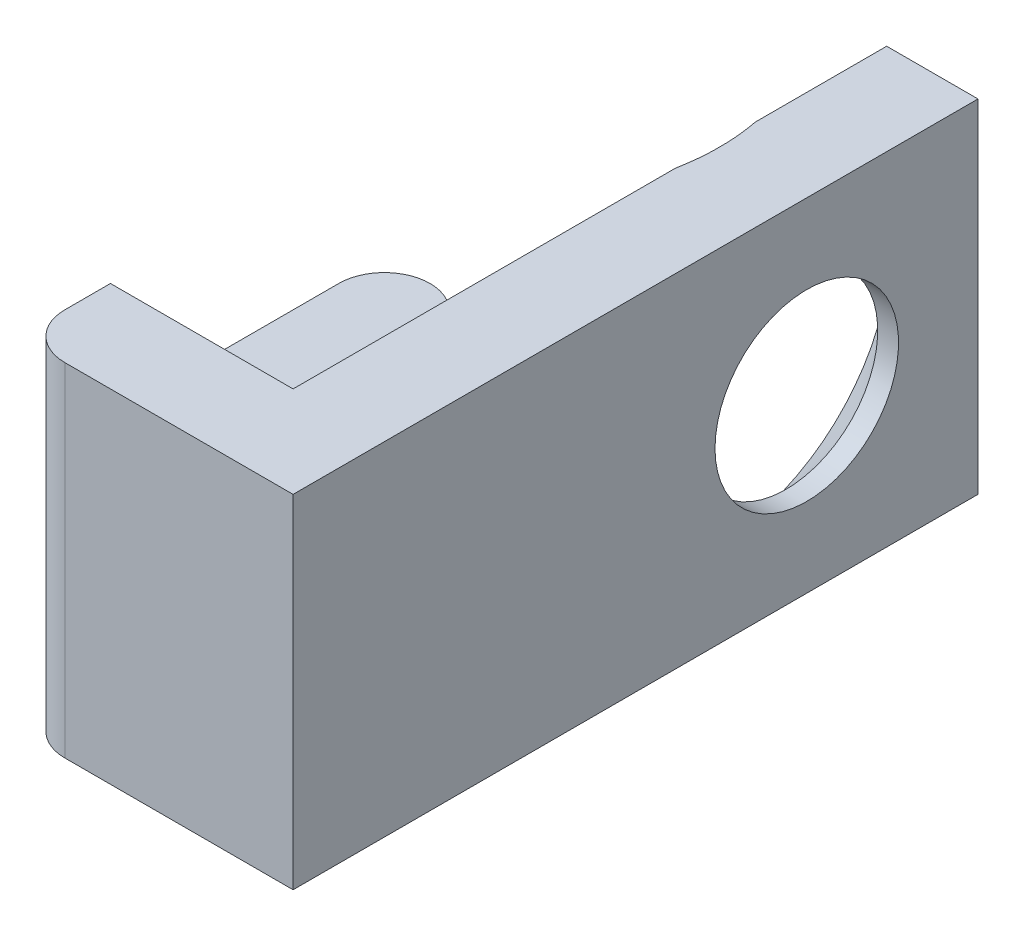
SolidWorks part; units mm, degrees
ref_plane "Front Plane" through (0, 0, 0) normal (0, 0, 1) x (1, 0, 0)
ref_plane "Top Plane" through (0, 0, 0) normal (0, 1, 0) x (1, 0, 0)
ref_plane "Right Plane" through (0, 0, 0) normal (1, 0, 0) x (0, 0, -1)
sketch "Sketch1" plane through (0, 0, 0) normal (0, 1, 0) x (1, 0, 0)
  line L0 (-1.27, -8.255) -> (-5.08, -8.255) construction
  line L1 (-1.27, -9.525) -> (1.27, -9.525)
  line L2 (-1.27, -9.525) -> (-1.27, 9.525)
  line L3 (-1.27, 9.525) -> (1.27, 9.525)
  line L4 (1.27, -9.525) -> (1.27, 9.525)
  line L5 (-1.27, -9.525) -> (1.27, 9.525) construction
  line L6 (-1.27, 9.525) -> (1.27, -9.525) construction
  line L7 (-1.27, -9.525) -> (-5.08, -9.525)
  line L8 (-1.27, -6.985) -> (-5.08, -6.985)
  line L9 (-5.08, -8.255) -> (-5.08, -0.635) construction
  line L10 (-6.35, -8.255) -> (-6.35, -0.635)
  line L11 (-3.81, -8.255) -> (-3.81, -0.635)
  arc A0 (-1.27, -9.525) -> (-1.27, -6.985) centre (-1.27, -8.255) ccw
  arc A1 (-5.08, -6.985) -> (-5.08, -9.525) centre (-5.08, -8.255) ccw
  arc A2 (-6.35, -8.255) -> (-3.81, -8.255) centre (-5.08, -8.255) ccw
  arc A3 (-3.81, -0.635) -> (-6.35, -0.635) centre (-5.08, -0.635) ccw
  point P0 (0, 0)
  point P8 (-3.175, -8.255)
  point P13 (-5.08, -4.445)
  point P20 (-3.9688, -2.2199)
  dimension "D1" = 2.54
  dimension "D2" = 19.05
  dimension "D3" = 2.54
  dimension "D4" = 2.54
  dimension "D5" = 6.35
extrude "Boss-Extrude1" add sketch "Sketch1" along normal mid plane 9.525 contours L11 A3 L10 A1 L8 | A1 A2 L11 L8 | A2 L7 L2 L8 L11 | L2 A0 | A0 L1 L4 L3 L2
sketch "Sketch2" plane through (-1.27, 0, 0) normal (-1, 0, 0) x (0, 0, 1)
  line L0 (-9.525, 0) -> (-4.7625, 0) construction
  line L1 (-9.525, 4.7625) -> (-9.525, -4.7625) construction
  line L2 (-9.525, -4.7625) -> (-4.7625, 0) construction
  line L3 (-4.7625, 0) -> (-9.525, 4.7625) construction
  point P10 (-4.7625, 0)
hole_wizard "CSK for #10 Flat Head Machine Screw (100)1" positions "3DSketch1" profile "Sketch3" countersink size "#10" standard "ANSI Inch" end condition through all
sketch3d "3DSketch1"
  point P0 (-1.27, 0, -4.7625)
sketch "Sketch3" plane through (-1.27, 0, -4.7625) normal (0, 1, 0) x (0, 0, 1)
  line L0 (0, 0) -> (0, 2.54)
  line L1 (0, 2.54) -> (2.5527, 2.54)
  line L2 (2.5527, 2.54) -> (2.5527, 1.9608)
  line L3 (2.5527, 1.9608) -> (4.8895, 0)
  line L5 (4.8895, 0) -> (0, 0)
  line L6 (-2.5527, 1.9608) -> (-4.8895, 0) construction
  line L11 (0, -6.35) -> (0, 107.95) construction
  dimension "Thru Hole Dia." = 5.1054
  dimension "Thru Hole Depth" = 2.54
  dimension "Near C'Sink Dia." = 9.779
  dimension "Near C'Sink Angle" = 100
sketch "Sketch4" plane through (0, 0, 0) normal (1, 0, 0) x (0, 0, -1)
  line L0 (0.635, -4.7625) -> (-3.81, -4.7625) construction
  line L1 (-8.255, -4.7625) -> (-0.635, -4.7625) construction
  line L2 (0.635, -7.9375) -> (-3.81, -7.9375)
  line L3 (0.635, -1.5875) -> (-3.81, -1.5875)
  line L4 (0.635, 4.7625) -> (-3.81, 4.7625) construction
  line L5 (-8.255, 4.7625) -> (-0.635, 4.7625) construction
  line L6 (0.635, 1.5875) -> (-3.81, 1.5875)
  line L7 (0.635, 7.9375) -> (-3.81, 7.9375)
  line L8 (-6.985, -4.7625) -> (-6.985, 4.7625) construction
  arc A0 (0.635, -7.9375) -> (0.635, -1.5875) centre (0.635, -4.7625) ccw
  arc A1 (-3.81, -1.5875) -> (-3.81, -7.9375) centre (-3.81, -4.7625) ccw
  arc A2 (0.635, 1.5875) -> (0.635, 7.9375) centre (0.635, 4.7625) ccw
  arc A3 (-3.81, 7.9375) -> (-3.81, 1.5875) centre (-3.81, 4.7625) ccw
  point P5 (-1.5875, -4.7625)
  point P10 (-1.5875, 4.7625)
  dimension "D1" = 3.175
extrude "Cut-Extrude1" cut sketch "Sketch4" against normal through all from surface at -1.27 starting at face at (-1.27, 0, 2.6104)
